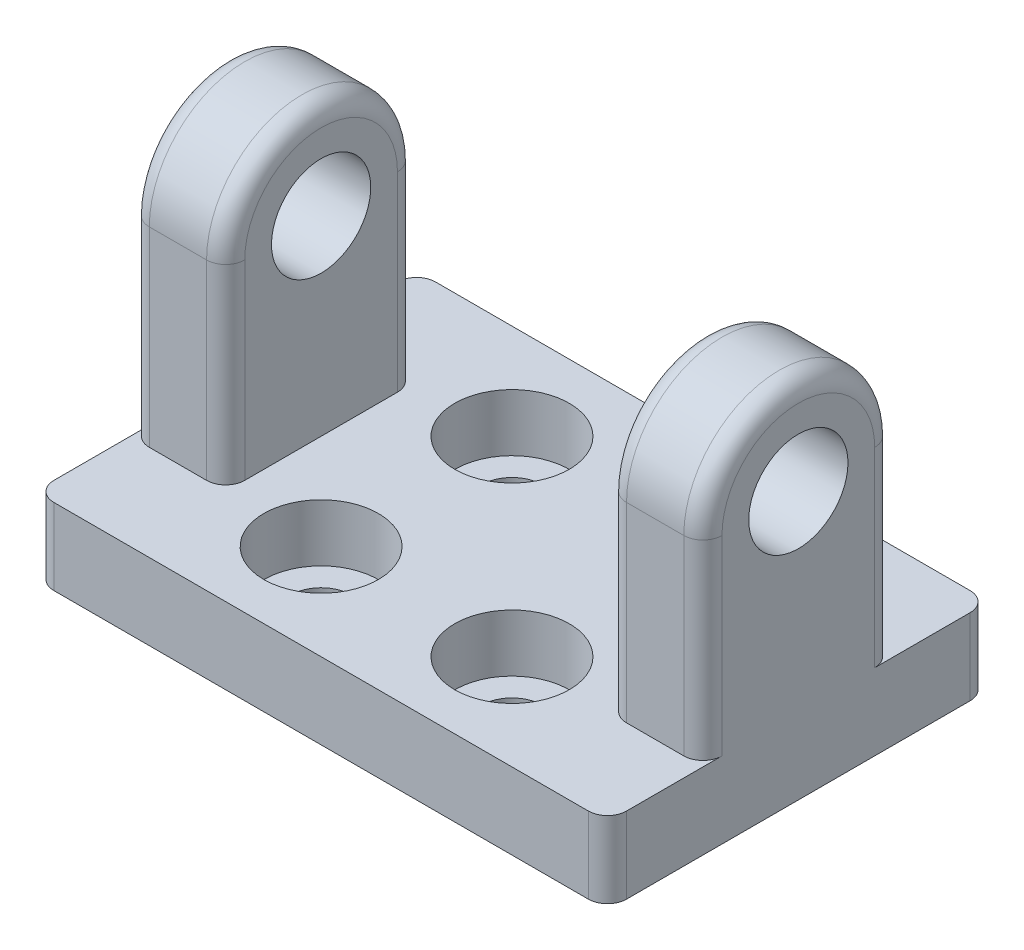
SolidWorks part; units mm, degrees
ref_plane "Plan de face" through (0, 0, 0) normal (0, 0, 1) x (1, 0, 0)
ref_plane "Plan de dessus" through (0, 0, 0) normal (0, 1, 0) x (1, 0, 0)
ref_plane "Plan de droite" through (0, 0, 0) normal (1, 0, 0) x (0, 0, -1)
sketch "Esquisse2" plane through (0, 0, 0) normal (1, 0, 0) x (0, 0, -1)
  line L0 (5, 0) -> (5, -10)
  line L2 (-5, 0) -> (-5, -10)
  line L3 (-5, -10) -> (5, -10)
  circle A0 centre (0, 0) radius 2.6
  arc A2 (5, 0) -> (-5, 0) centre (0, 0) ccw
  dimension "D1" = 5.2
  dimension "D2" = 10
  dimension "D3" = 5
  dimension "D4" = 5
extrude "Boss.-Extru.1" add sketch "Esquisse2" along normal mid plane 30
sketch "Esquisse4" plane through (0, -10, 0) normal (0, -1, 0) x (1, 0, 0)
  line L0 (-15, 5) -> (-15, -5) construction
  line L1 (-15, -10) -> (15, -10)
  line L2 (-15, -10) -> (-15, 10)
  line L3 (-15, 10) -> (15, 10)
  line L4 (15, -10) -> (15, 10)
  line L5 (15, 5) -> (15, -5) construction
  dimension "D1" = 20
  dimension "D4" = 10
extrude "Boss.-Extru.2" add sketch "Esquisse4" along normal blind 4
sketch "Esquisse5" plane through (0, -10, 0) normal (0, 1, 0) x (1, 0, 0)
  circle A0 centre (5, -5) radius 1.6
  circle A1 centre (5, 5) radius 1.6
  circle A2 centre (-5, 5) radius 1.6
  circle A3 centre (-5, -5) radius 1.6
  point P15 (0, 0)
  dimension "D1" = 3.2
  dimension "D2" = 10
  dimension "D3" = 10
  dimension "D4" = 5
  dimension "D5" = 5
extrude "Enlèv. mat.-Extru.1" cut sketch "Esquisse5" against normal up to next contours A0
sketch "Esquisse6" plane through (0, 0, 5) normal (0, 0, 1) x (1, 0, 0)
  line L0 (15, -10) -> (6.6, -10) construction
  line L1 (-10, 11.5437) -> (10, 11.5437)
  line L2 (-10, 11.5437) -> (-10, -10)
  line L3 (-10, -10) -> (10, -10)
  line L4 (10, 11.5437) -> (10, -10)
  line L5 (15, 0) -> (-15, 0) construction
  point P7 (0, 11.5437)
  point P11 (0, 0)
  dimension "D2" = 20
extrude "Enlèv. mat.-Extru.2" cut sketch "Esquisse6" against normal through all
sketch "Esquisse7" plane through (0, -10, 0) normal (0, 1, 0) x (1, 0, 0)
  circle A4 centre (-5, 5) radius 3
  circle A5 centre (5, 5) radius 3
  circle A6 centre (5, -5) radius 3
  circle A7 centre (-5, -5) radius 3
  dimension "D1" = 6
extrude "Enlèv. mat.-Extru.3" cut sketch "Esquisse7" against normal blind 3
fillet "Congé1" radius 1 16 edges at (10, -5, -5) (10, -5, 5) (-10, -5, 5) (-10, -5, -5) (15, -5, -5) (15, -5, 5) (-15, -5, -5) (-15, -5, 5) (10, 5, 0) (-10, 5, 0) (15, 5, 0) (-15, 5, 0) (-15, -12, -10) (-15, -12, 10) (15, -12, -10) (15, -12, 10)
